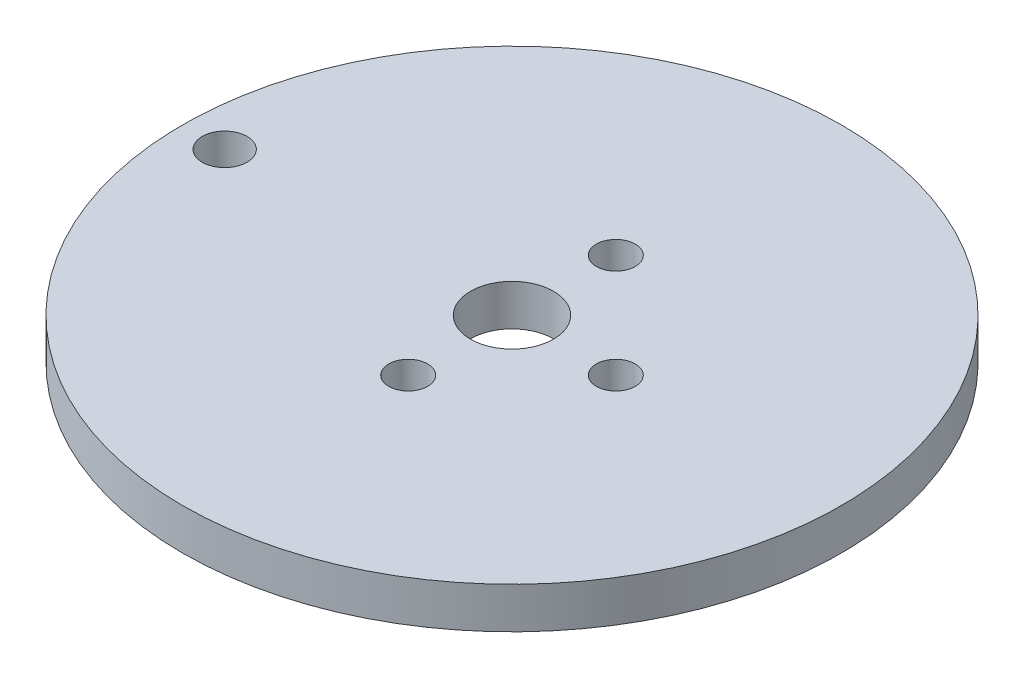
SolidWorks part; units mm, degrees
ref_plane "Front Plane" through (0, 0, 0) normal (0, 0, 1) x (1, 0, 0)
ref_plane "Top Plane" through (0, 0, 0) normal (0, 1, 0) x (1, 0, 0)
ref_plane "Right Plane" through (0, 0, 0) normal (1, 0, 0) x (0, 0, -1)
sketch "Sketch1" plane through (0, 0, 0) normal (0, 1, 0) x (1, 0, 0)
  circle A0 centre (0, 0) radius 25.4
  dimension "D1" = 50.8
extrude "Boss-Extrude1" add sketch "Sketch1" along normal blind 3.175
sketch "Sketch2" plane through (0, 3.175, 0) normal (0, 1, 0) x (1, 0, 0)
  line L0 (-22.145, 0) -> (0, 0) construction
  circle A0 centre (-22.145, 0) radius 1.7272
  dimension "D2" = 3.4544
  dimension "D1" = 22.145
extrude "Cut-Extrude1" cut sketch "Sketch2" against normal through all
sketch "Sketch3" plane through (0, 3.175, 0) normal (0, 1, 0) x (1, 0, 0)
  circle A0 centre (0, 0) radius 3.2004
  dimension "D1" = 6.4008
extrude "Cut-Extrude2" cut sketch "Sketch3" against normal through all
sketch "Sketch4" plane through (0, 3.175, 0) normal (0, 1, 0) x (1, 0, 0)
  line L0 (0, 8) -> (0, -8) construction
  line L1 (8, 0) -> (-8, 0) construction
  circle A0 centre (0, 0) radius 8 construction
  circle A1 centre (0, 8) radius 1.5
  circle A2 centre (0, -8) radius 1.5
  circle A3 centre (8, 0) radius 1.5
  dimension "D1" = 16
  dimension "D2" = 3
  dimension "D3" = 3
  dimension "D4" = 3
extrude "Cut-Extrude3" cut sketch "Sketch4" against normal through all
